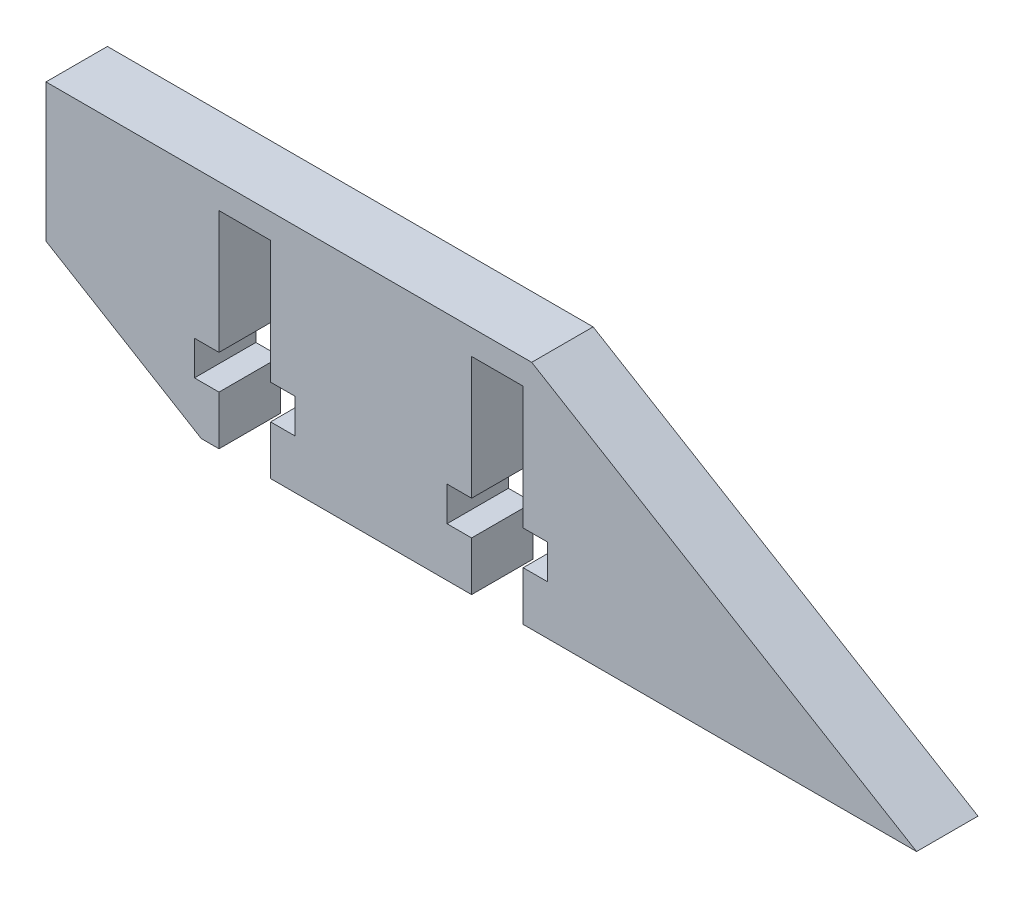
SolidWorks part; units mm, degrees
ref_plane "Front Plane" through (0, 0, 0) normal (0, 0, 1) x (1, 0, 0)
ref_plane "Top Plane" through (0, 0, 0) normal (0, 1, 0) x (1, 0, 0)
ref_plane "Right Plane" through (0, 0, 0) normal (1, 0, 0) x (0, 0, -1)
sketch "Sketch3" plane through (0, 0, -218) normal (0, 0, 1) x (1, 0, 0)
  line L1 (-321.3873, 435.8394) -> (-219.1873, 374.4314) construction
  line L4 (-278.9806, 371.8599) -> (-352.9324, 416.2947) construction
  line L5 (-282.0394, 408.6968) -> (-340.2875, 408.6968)
  line L7 (-352.9324, 416.2947) -> (-352.9324, 550.3534) construction
  line L8 (-340.2875, 408.6968) -> (-352.9324, 416.2947)
  line L9 (-352.9324, 416.2947) -> (-352.9324, 427.5284)
  line L12 (-352.9324, 427.5284) -> (-313.3804, 427.5284)
  line L17 (-313.3804, 427.5284) -> (-282.0394, 408.6968)
  line L19 (-256.5325, 289.7456) -> (-300.6394, 401.3457) construction
  line L20 (-256.5325, 289.7456) -> (-237.9324, 297.0968) construction
  line L21 (-300.6394, 401.3457) -> (-282.0394, 408.6968) construction
  line L22 (-322.9324, 433.2679) -> (-220.7324, 371.8599) construction
  line L23 (-237.9324, 297.0968) -> (-282.0394, 408.6968) construction
  line L24 (-237.9324, 555.2679) -> (-237.9324, 302.8679) construction
  point P2 (0, 0)
  dimension "D1" = 20
  dimension "D2" = 120
extrude "Boss-Extrude1" add sketch "Sketch3" against normal blind 5
sketch "Sketch4" plane through (0, 0, -223) normal (0, 0, -1) x (-1, 0, 0)
  line L12 (318.2758, 408.6968) -> (314.0758, 408.6968)
  line L13 (318.2758, 408.6968) -> (318.2758, 412.6968)
  line L14 (314.0758, 408.6968) -> (314.0758, 412.6968)
  line L15 (320.2758, 412.6968) -> (318.2758, 412.6968)
  line L16 (320.2758, 412.6968) -> (320.2758, 415.4968)
  line L17 (312.0758, 412.6968) -> (312.0758, 415.4968)
  line L18 (320.2758, 415.4968) -> (318.2758, 415.4968)
  line L19 (318.2758, 415.4968) -> (318.2758, 425.4968)
  line L20 (314.0758, 415.4968) -> (314.0758, 425.4968)
  line L21 (318.2758, 425.4968) -> (314.0758, 425.4968)
  line L22 (314.0758, 415.4968) -> (312.0758, 415.4968)
  line L23 (314.0758, 412.6968) -> (312.0758, 412.6968)
  line L24 (316.1758, 425.4968) -> (316.1758, 421.1685) construction
  line L25 (340.2875, 408.6968) -> (282.0394, 408.6968) construction
  line L26 (282.0394, 408.6968) -> (340.2875, 408.6968) construction
  line L28 (305.8916, 421.1685) -> (326.4599, 421.1685) construction
  line L29 (336.744, 425.4968) -> (336.744, 421.1685) construction
  line L30 (326.4599, 421.1685) -> (326.4599, 417.0182) construction
  line L31 (338.844, 412.6968) -> (340.844, 412.6968)
  line L32 (338.844, 415.4968) -> (340.844, 415.4968)
  line L33 (334.644, 425.4968) -> (338.844, 425.4968)
  line L34 (338.844, 415.4968) -> (338.844, 425.4968)
  line L35 (334.644, 415.4968) -> (334.644, 425.4968)
  line L36 (332.644, 415.4968) -> (334.644, 415.4968)
  line L37 (340.844, 412.6968) -> (340.844, 415.4968)
  line L38 (332.644, 412.6968) -> (332.644, 415.4968)
  line L39 (332.644, 412.6968) -> (334.644, 412.6968)
  line L40 (338.844, 408.6968) -> (338.844, 412.6968)
  line L41 (334.644, 408.6968) -> (334.644, 412.6968)
  line L42 (334.644, 408.6968) -> (338.844, 408.6968)
  point P14 (319.0985, 408.6968)
  point P16 (325.9402, 425.4968)
  point P20 (302.8169, 425.4968)
  point P29 (0, 0)
  point P30 (326.4599, 408.6968)
  point P40 (0, 0)
  point P41 (0, 0)
  point P43 (318.2758, 425.4968)
  dimension "D1" = 4.2
  dimension "D2" = 2
  dimension "D3" = 2
  dimension "D4" = 2.8
  dimension "D5" = 10
  dimension "D6" = 4
extrude "Cut-Extrude1" cut sketch "Sketch4" against normal through all both and the other way through all
